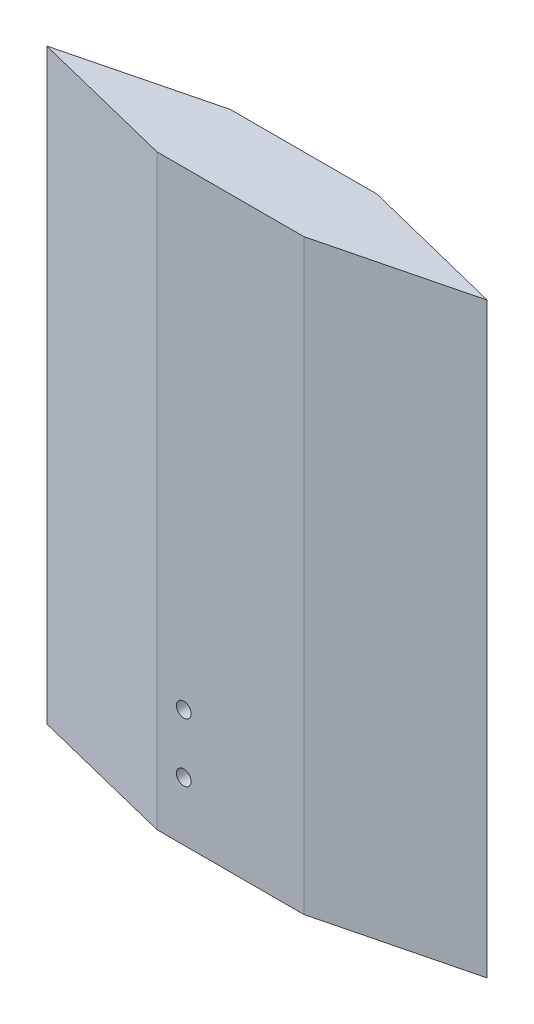
SolidWorks part; units mm, degrees
ref_plane "Front Plane" through (0, 0, 0) normal (0, 0, 1) x (1, 0, 0)
ref_plane "Top Plane" through (0, 0, 0) normal (0, 1, 0) x (1, 0, 0)
ref_plane "Right Plane" through (0, 0, 0) normal (1, 0, 0) x (0, 0, -1)
sketch "Sketch1" plane through (0, 0, 0) normal (0, 1, 0) x (1, 0, 0)
  line L0 (0, 6.35) -> (-12.7, 3.1623)
  line L1 (0, 0) -> (12.7, 0)
  line L3 (0, 6.35) -> (12.7, 6.35)
  line L5 (-12.7, 3.1623) -> (0, 0)
  line L6 (12.7, 0) -> (25.4, 3.175)
  line L7 (25.4, 3.175) -> (12.7, 6.35)
  dimension "D1" = 12.7
  dimension "D2" = 6.35
  dimension "D5" = 3.1877
  dimension "D6" = 3.175
extrude "Boss-Extrude1" add sketch "Sketch1" along normal blind 50.8
sketch "Sketch2" plane through (0, 0, 0) normal (0, -1, 0) x (1, 0, 0)
  line L0 (0, 0) -> (12.7, 0) construction
  line L1 (3.175, -2.54) -> (3.175, -3.81)
  line L2 (3.175, -3.81) -> (1.455, -3.81)
  line L3 (3.175, -2.54) -> (1.455, -2.54)
  arc A0 (1.455, -2.54) -> (1.455, -3.81) centre (0, -3.175) ccw
  dimension "D1" = 3.175
  dimension "D2" = 3.175
  dimension "D3" = 0.635
  dimension "D4" = 1.27
  dimension "D5" = 3.175
  dimension "D6" = 12.7
extrude "Cut-Extrude1" cut sketch "Sketch2" against normal blind 16.51
sketch "Sketch3" plane through (0, 0, 0) normal (0, 0, 1) x (1, 0, 0)
  line L0 (0, 0) -> (12.7, 0) construction
  line L1 (0, 50.8) -> (0, 0) construction
  circle A0 centre (2.3152, 5.08) radius 0.635
  circle A1 centre (2.3152, 10.16) radius 0.635
  dimension "D1" = 1.27
  dimension "D2" = 5.08
  dimension "D3" = 2.3152
  dimension "D4" = 2
extrude "Cut-Extrude2" cut sketch "Sketch3" against normal blind 3.175
